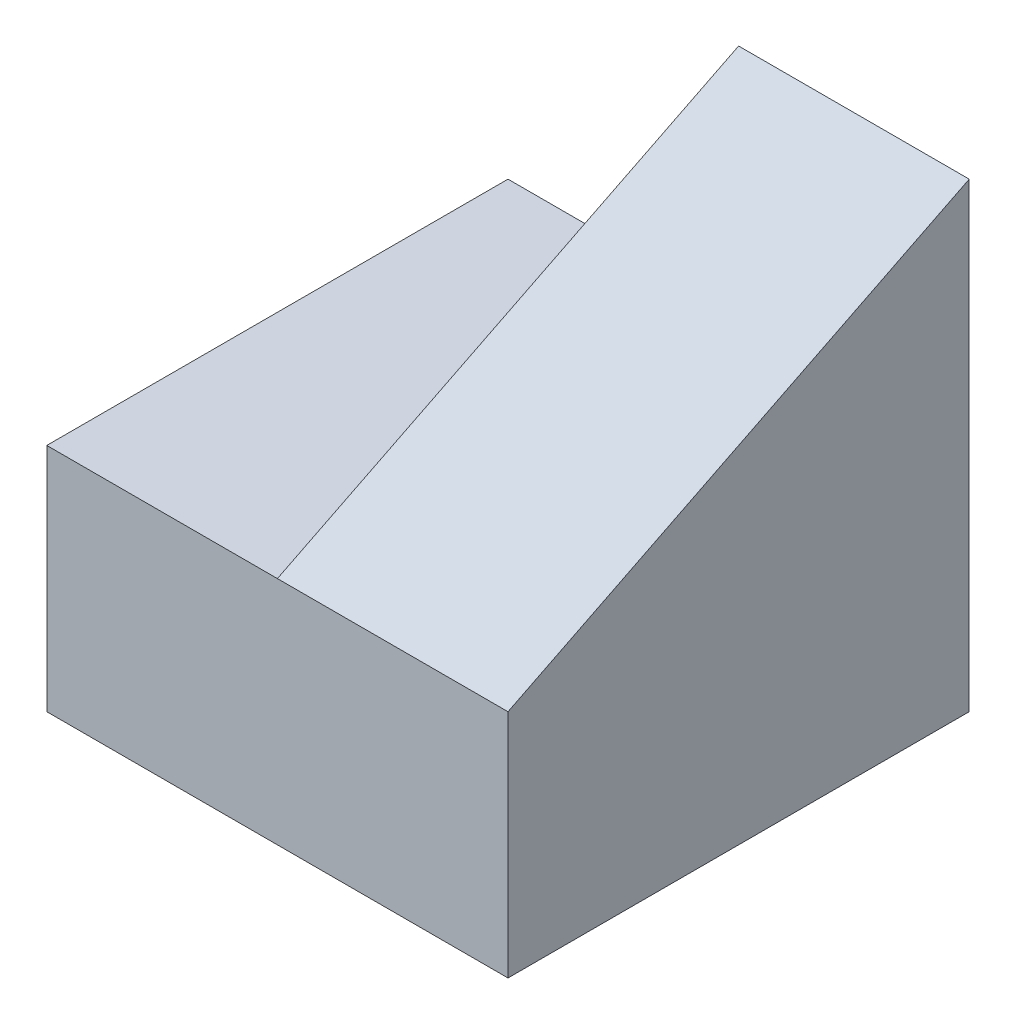
SolidWorks part; units mm, degrees
ref_plane "Front Plane" through (0, 0, 0) normal (0, 0, 1) x (1, 0, 0)
ref_plane "Top Plane" through (0, 0, 0) normal (0, 1, 0) x (1, 0, 0)
ref_plane "Right Plane" through (0, 0, 0) normal (1, 0, 0) x (0, 0, -1)
sketch "Sketch1" plane through (0, 0, 0) normal (0, 0, 1) x (1, 0, 0)
  line L1 (0, 0) -> (40, 0)
  line L2 (0, 0) -> (0, 20)
  line L3 (0, 20) -> (40, 20)
  line L4 (40, 0) -> (40, 20)
  dimension "D1" = 40
  dimension "D2" = 20
extrude "Boss-Extrude1" add sketch "Sketch1" along normal blind 40
sketch "Sketch2" plane through (40, 0, 0) normal (1, 0, 0) x (0, 0, -1)
  line L0 (-40, 20) -> (0, 20)
  line L1 (0, 20) -> (0, 40)
  line L2 (0, 40) -> (-40, 20)
  dimension "D1" = 20
extrude "Boss-Extrude2" add sketch "Sketch2" against normal blind 20
